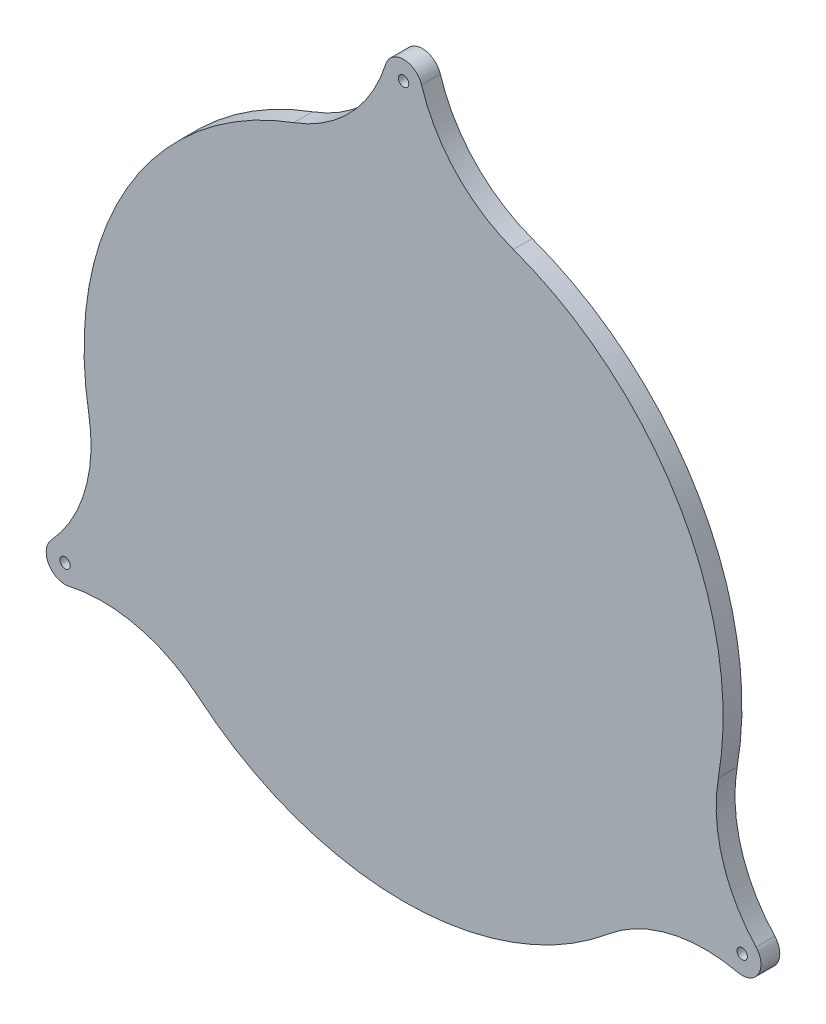
SolidWorks part; units mm, degrees
material "6061-T6 Black anodised"
ref_plane "Front Plane" through (0, 0, 0) normal (0, 0, 1) x (1, 0, 0)
ref_plane "Top Plane" through (0, 0, 0) normal (0, 1, 0) x (1, 0, 0)
ref_plane "Right Plane" through (0, 0, 0) normal (1, 0, 0) x (0, 0, -1)
sketch "Sketch1" plane through (0, 0, 0) normal (0, 0, 1) x (1, 0, 0)
  arc A0 (-29.2151, 79.8215) -> (-83.735, -14.6098) centre (0, 0) ccw
  circle A1 centre (0, 104) radius 1.375
  arc A2 (4.7737, 105.4872) -> (-4.7737, 105.4872) centre (0, 104) ccw
  arc A3 (4.7737, 105.4872) -> (29.2151, 79.8215) centre (42.9634, 117.3846) ccw
  arc A4 (-4.7737, 105.4872) -> (-29.2151, 79.8215) centre (-42.9634, 117.3846) cw
  arc A5 (93.7414, -48.6094) -> (83.735, -14.6098) centre (123.1397, -21.4849) cw
  arc A6 (88.9677, -56.8777) -> (54.5199, -65.2118) centre (80.1764, -95.8997) ccw
  circle A7 centre (90.0666, -52) radius 1.375
  arc A8 (88.9677, -56.8777) -> (93.7414, -48.6094) centre (90.0666, -52) ccw
  arc A9 (-88.9677, -56.8777) -> (-54.5199, -65.2118) centre (-80.1764, -95.8997) cw
  arc A10 (-93.7414, -48.6094) -> (-83.735, -14.6098) centre (-123.1397, -21.4849) ccw
  circle A11 centre (-90.0666, -52) radius 1.375
  arc A12 (-93.7414, -48.6094) -> (-88.9677, -56.8777) centre (-90.0666, -52) ccw
  arc A13 (83.735, -14.6098) -> (29.2151, 79.8215) centre (0, 0) ccw
  arc A14 (-54.5199, -65.2118) -> (54.5199, -65.2118) centre (0, 0) ccw
  circle A15 centre (0, 92) radius 1.6 construction
  circle A16 centre (79.6743, -46) radius 1.6 construction
  circle A17 centre (-79.6743, -46) radius 1.6 construction
  point P29 (0, 0)
  point P36 (0, 0)
  dimension "D1" = 170
  dimension "D3" = 2.75
  dimension "D4" = 5
  dimension "D5" = 40
  dimension "D8" = 3.2
  dimension "D2" = 104
  dimension "D7" = 92
  dimension "D6" = 3
  dimension "D9" = 3
extrude "Boss-Extrude1" add sketch "Sketch1" along normal blind 5
sketch "Sketch2" plane through (0, 0, 5) normal (0, 0, 1) x (1, 0, 0)
  line L0 (0, 75) -> (64.9519, -37.5) construction
  line L1 (64.9519, -37.5) -> (-64.9519, -37.5) construction
  line L2 (-64.9519, -37.5) -> (0, 75) construction
  line L3 (64.9519, -37.5) -> (0, 0) construction
  line L4 (-64.9519, -37.5) -> (0, 0) construction
  line L5 (0, 75) -> (0, -75) construction
  line L6 (-32.476, 18.75) -> (-64.9519, 37.5) construction
  line L7 (32.476, 18.75) -> (64.9519, 37.5) construction
  line L9 (-37.5, 64.9519) -> (-75, 0)
  line L10 (-75, 0) -> (-37.5, -64.9519)
  line L11 (-37.5, -64.9519) -> (37.5, -64.9519)
  line L12 (37.5, -64.9519) -> (75, 0)
  line L13 (75, 0) -> (37.5, 64.9519)
  line L14 (37.5, 64.9519) -> (-37.5, 64.9519)
  circle A0 centre (0, 0) radius 75 construction
  circle A1 centre (0, 0) radius 75 construction
  point P0 (0, 75)
  point P6 (64.9519, -37.5)
  point P7 (-64.9519, -37.5)
  point P8 (0, 0)
  point P10 (-32.476, 18.75)
  point P11 (32.476, 18.75)
  point P12 (0, -37.5)
  point P18 (32.476, -18.75)
  point P19 (-32.476, -18.75)
  dimension "D1" = 150
  dimension "D3" = 120
  dimension "D4" = 120
  dimension "D5" = 64.9519
  dimension "D6" = 18.75
  dimension "D7" = 32.476
  dimension "D8" = 18.75
  dimension "D9" = 32.476
  dimension "D10" = 37.5
  dimension "D11" = 37.5
  dimension "D12" = 64.9519
  dimension "D13" = 37.5
  dimension "D14" = 75
  dimension "D2" = 3
